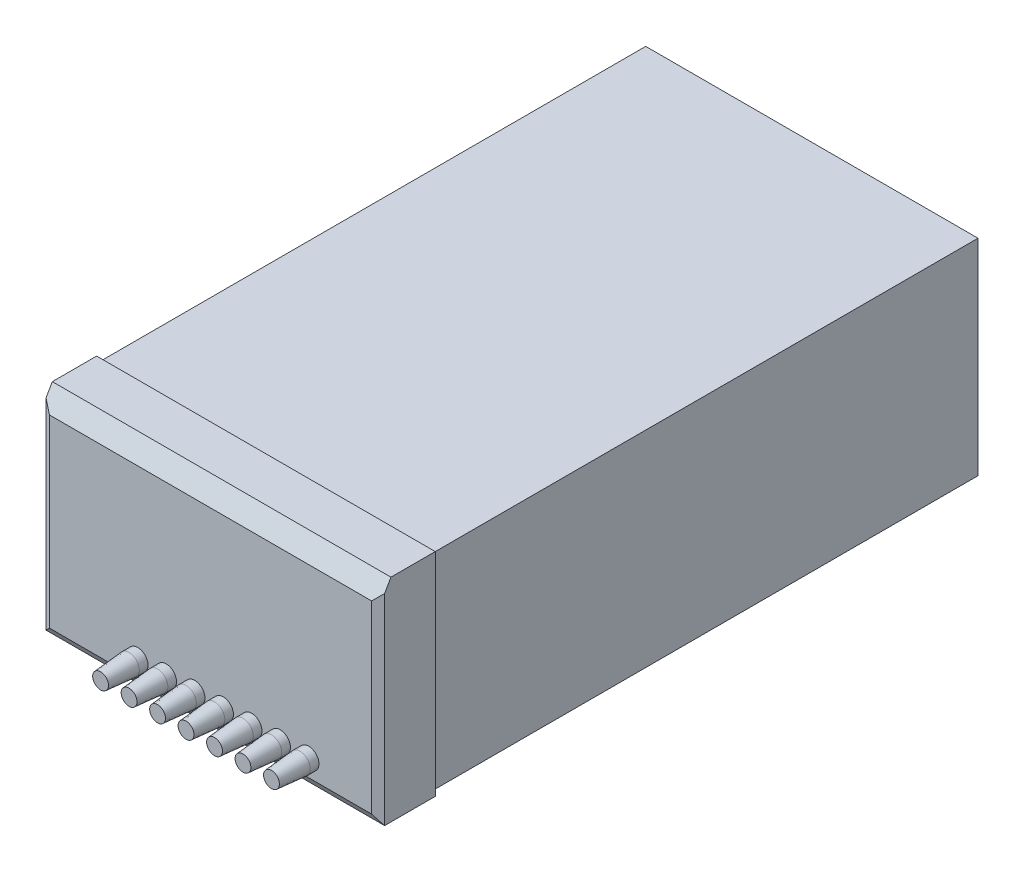
SolidWorks part; units mm, degrees
ref_plane "Front Plane" through (0, 0, 0) normal (0, 0, 1) x (1, 0, 0)
ref_plane "Top Plane" through (0, 0, 0) normal (0, 1, 0) x (1, 0, 0)
ref_plane "Right Plane" through (0, 0, 0) normal (1, 0, 0) x (0, 0, -1)
sketch "Sketch1" plane through (0, 0, 0) normal (0, 0, 1) x (1, 0, 0)
  line L1 (-105, -65) -> (105, -65)
  line L2 (-105, -65) -> (-105, 65)
  line L3 (-105, 65) -> (105, 65)
  line L4 (105, -65) -> (105, 65)
  line L5 (-105, -65) -> (105, 65) construction
  line L6 (-105, 65) -> (105, -65) construction
  point P0 (0, 0)
  dimension "D1" = 210
  dimension "D2" = 130
extrude "Boss-Extrude1" add sketch "Sketch1" against normal blind 345
sketch "Sketch2" plane through (0, 0, 0) normal (0, 0, 1) x (1, 0, 0)
  line L8 (107, -67) -> (107, 67)
  line L9 (107, 67) -> (-107, 67)
  line L10 (-107, 67) -> (-107, -67)
  line L11 (-107, -67) -> (107, -67)
  line L12 (107, -67) -> (107, 67)
  line L13 (107, 67) -> (-107, 67)
  line L14 (-107, 67) -> (-107, -67)
  line L15 (-107, -67) -> (107, -67)
  dimension "D1" = 2
extrude "Boss-Extrude2" add sketch "Sketch2" along normal blind 35 separate body
chamfer "Chamfer2" distance 7 angle 60 1 edges at (0, 67, 35)
chamfer "Chamfer3" distance 3 angle 60 3 edges at (107, -6.0622, 35) (0, -67, 35) (-107, -6.0622, 35)
sketch "Sketch3" plane through (0, 0, 35) normal (0, 0, 1) x (1, 0, 0)
  line L0 (107, 60.0718) -> (107, -67) construction
  line L1 (107, -67) -> (-107, -67) construction
  circle A0 centre (-46, -51) radius 6.5
  circle A1 centre (-28, -51) radius 6.5
  circle A2 centre (-10, -51) radius 6.5
  circle A3 centre (8, -51) radius 6.5
  circle A4 centre (26, -51) radius 6.5
  circle A5 centre (44, -51) radius 6.5
  circle A6 centre (62, -51) radius 6.5
  dimension "D1" = 13
  dimension "D2" = 16
  dimension "D4" = 18
  dimension "D5" = 45
  dimension "D3" = 7
extrude "Boss-Extrude3" add sketch "Sketch3" along normal blind 5.5 separate body
ref_plane "Plane1" through (0, 0, 40.5) normal (0, 0, 1) x (1, 0, 0)
ref_plane "Plane2" through (0, 0, 58.5) normal (0, 0, 1) x (1, 0, 0)
sketch "Sketch5" plane through (0, 0, 40.5) normal (0, 0, 1) x (1, 0, 0)
  circle A0 centre (62, -51) radius 6.5 construction
  circle A1 centre (44, -51) radius 6.5 construction
  circle A2 centre (26, -51) radius 6.5 construction
  circle A3 centre (8, -51) radius 6.5 construction
  circle A4 centre (-10, -51) radius 6.5 construction
  circle A5 centre (-28, -51) radius 6.5 construction
  circle A6 centre (-46, -51) radius 6.5 construction
  circle A7 centre (62, -51) radius 6.5
  circle A8 centre (44, -51) radius 6.5
  circle A9 centre (26, -51) radius 6.5
  circle A10 centre (8, -51) radius 6.5
  circle A11 centre (-10, -51) radius 6.5
  circle A12 centre (-28, -51) radius 6.5
  circle A13 centre (-46, -51) radius 6.5
sketch "Sketch6" plane through (0, 0, 58.5) normal (0, 0, 1) x (1, 0, 0)
  circle A0 centre (-46, -51) radius 5
  circle A1 centre (-28, -51) radius 5
  circle A2 centre (-10, -51) radius 5
  circle A3 centre (8, -51) radius 5
  circle A4 centre (26, -51) radius 5
  circle A5 centre (44, -51) radius 5
  circle A6 centre (62, -51) radius 5
  dimension "D1" = 10
  dimension "D3" = 18
  dimension "D2" = 7
loft "Loft1" add section "Sketch5" section "Sketch6"
pattern_linear "LPattern1" count 7 spacing 18 along (1, 0, 0) of "Loft1"
